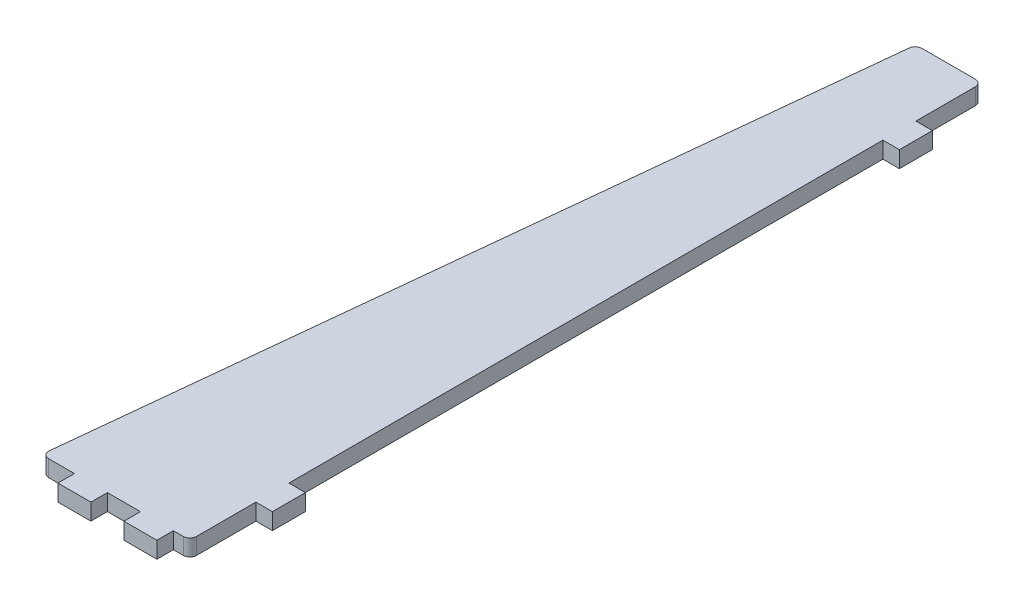
SolidWorks part; units mm, degrees
material "Beech"
ref_plane "Front Plane" through (0, 0, 0) normal (0, 0, 1) x (1, 0, 0)
ref_plane "Top Plane" through (0, 0, 0) normal (0, 1, 0) x (1, 0, 0)
ref_plane "Right Plane" through (0, 0, 0) normal (1, 0, 0) x (0, 0, -1)
sketch "Sketch1" plane through (0, 0, 0) normal (0, 1, 0) x (1, 0, 0)
  line L0 (0, 0) -> (12.7, 0)
  line L1 (12.7, 0) -> (12.7, -6.35)
  line L2 (12.7, -6.35) -> (25.4, -6.35)
  line L3 (25.4, -6.35) -> (25.4, 0)
  line L4 (25.4, 0) -> (38.1, 0)
  line L5 (38.1, 0) -> (38.1, -6.35)
  line L6 (38.1, -6.35) -> (50.8, -6.35)
  line L7 (50.8, -6.35) -> (50.8, 0)
  line L8 (50.8, 0) -> (57.15, 0)
  line L9 (57.15, 0) -> (57.15, 25.4)
  line L10 (57.15, 304.8) -> (31.75, 304.8)
  line L11 (31.75, 304.8) -> (0, 0)
  line L12 (57.15, 25.4) -> (63.5, 25.4)
  line L13 (63.5, 25.4) -> (63.5, 38.1)
  line L14 (63.5, 38.1) -> (57.15, 38.1)
  line L15 (57.15, 38.1) -> (57.15, 266.7)
  line L16 (57.15, 266.7) -> (63.5, 266.7)
  line L17 (63.5, 266.7) -> (63.5, 279.4)
  line L18 (63.5, 279.4) -> (57.15, 279.4)
  line L19 (57.15, 279.4) -> (57.15, 304.8)
  dimension "D1" = 12.7
  dimension "D2" = 6.35
  dimension "D3" = 25.4
  dimension "D4" = 25.4
  dimension "D5" = 12.7
  dimension "D6" = 304.8
  dimension "D7" = 25.4
  dimension "D8" = 25.4
  dimension "D9" = 6.35
extrude "Side Plate" add sketch "Sketch1" along normal blind 6.35
fillet "Fillet1" radius 2.54 4 edges at (57.15, 3.175, 0) (57.15, 3.175, -304.8) (31.75, 3.175, -304.8) (0, 3.175, 0)
equation "\"CageLeftBottomEdge\"=22.11mm"
equation "\"CageLeftTopEdge\"=22.11mm"
equation "\"CageRightBottomEdge\"=21.63mm"
equation "\"CageRightTopEdge\"=21.63mm"
equation "\"CageHeight\"=86.04mm"
equation "\"CageLength\"=73.76mm"
equation "\"CageTopScrewClearance\"=10mm"
equation "\"CageBottomScrewClearance\"=25mm"
equation "\"CageLeftTopDepth\"= 11.65mm"
equation "\"CageLeftBottomDepth\"=11.11mm"
equation "\"CageLeftTopHeight\"=8.56175mm"
equation "\"CageLeftBottomHeight\"=16mm"
equation "\"CageRightTopDepth\"= 11.05mm"
equation "\"CageRightBottomDepth\"=10.58mm"
equation "\"CageRightTopHeight\"=9.6mm"
equation "\"CageRightBottomHeight\"=15.49mm"
equation "\"CageLeftTopChannelDepth\"=2.41908mm"
equation "\"CageLeftBottomChannelDepth\"=2.588mm"
equation "\"CageLeftChannelHeight\"=11.7mm"
equation "\"CageRightTopChannelDepth\"=2.32mm"
equation "\"CageRightBottomChannelDepth\"=2.318mm"
equation "\"CageRightChannelHeight\"=10mm"
equation "\"CageChanRelHeight\"=23.99mm"
equation "\"CageChanRelDepth\"=5.492mm"
equation "\"CageChamberRadius\"=16.261mm"
equation "\"CageScrewDiameter\"=4.8mm"
equation "\"CageSetScrewDiameter\"=3.5mm"
equation "\"CageAxleRadius\"=6.639mm"
equation "\"CageAxleKeyHeight\"=1.619mm"
equation "\"CageAxleKeyWidth\"=2.662mm"
equation "\"CageHoseWindowWidth\"=16.29mm"
equation "\"CageHoseWindowHeight\"=26.5mm"
equation "\"CageHoseWindow-Edge\"=8.89mm"
equation "\"CageScrew-VerticalEdge\"=5.0mm"
equation "\"CageScrew-HorizontalEdge\"=7.5mm"
equation "\"CageScrew-HoseCornerScrewEdge\"=4.45mm"
equation "\"CageAxle-BottomEdge\"=56.05mm"
equation "\"CageAxle-FrontEdge\"=46.03mm"
equation "\"CageBackSetScrew-Axle\"=40mm"
equation "\"CageFrontSetScrew-Axle\"=22mm"
equation "\"CageVelocityWindow-BackEdge\"=34.8mm"
equation "\"CageVelocityWindow-BottomEdge\"=27.55mm"
equation "\"CageVelocityWindowHeight\"=22.29mm"
equation "\"CageVelocityWindowWidth\"=12.61mm"
equation "\"TriggerSlot-BottomEdge\"=6.35mm"
equation "\"TriggerSlot-FrontEdge\"=15mm"
equation "\"TriggerSlotSize\"=6.7mm"
equation "\"TriggerRackOffset\"=6mm"
equation "\"TriggerSlotSizeInt\"=.25in"
equation "\"MotorMountLegLength\"=.25in"
equation "\"GearOffset\"=.264907in"
equation "\"TriggerSlotSpacing\"=.25in"
equation "\"TriggerMiniSlotWidth\"=3.5mm"
equation "\"TriggerRackWidth\"=6.5mm"
equation "\"pandiscradius\"=14in"
equation "\"towermaterialwidth\"=.25in"
equation "\"towerslotlength\"=.5in"
equation "\"towermarkerspace\"=5in"
equation "\"towerslothorizoffset\"=1in"
equation "\"towerslothorizspacing\"=2in"
equation "\"towerslotvertoffset\"=3in"
equation "\"D1@Sketch1\"=\"towerslotlength\""
equation "\"D2@Sketch1\"=\"towermaterialwidth\""
equation "\"towerupslot\"=1in"
equation "\"D3@Sketch1\"=\"towerupslot\""
equation "\"towerslotvertspacing\"=1in"
equation "\"D4@Sketch1\"=\"towerslotvertspacing\""
equation "\"D5@Sketch1\"=\"towerslotlength\""
equation "\"towerheight\"=12in"
equation "\"D6@Sketch1\"=\"towerheight\""
equation "\"D7@Sketch1\"=\"towerslotlength\"*2"
equation "\"D8@Sketch1\"=\"towerupslot\""
equation "\"D9@Sketch1\"=\"towerslotvertoffset\"-(\"towermarkerspace\"/2)-\"towermaterialwidth\""
equation "\"D1@Side Plate\"=\"towermaterialwidth\""
equation "\"toweraxle\"=.5in"
equation "\"stepperouterrad\"=10mm"
equation "\"stepperscrewsize\"=3.45mm"
equation "\"stepperscrewc2c\"=49.5mm"
equation "\"stepperdepthoffset\"=24mm"
equation "\"stepperhorizoffset\"=22.91mm"
equation "\"shaftslotOD\"=18.8mm"
equation "\"shaftslotID\"=13.28mm"
equation "\"shaftkeywidth\"=2.67mm"
equation "\"shaftkeydepth\"=1.8mm"
equation "\"shaftcollartotaldepth\"=12.5mm"
equation "\"shaftsquaredepth\"=6mm"
equation "\"shaftsetscrewsize\"=3.5mm"
equation "\"shaftkeytightdepth\"=1.85mm"
equation "\"shaftslottightID\"=12.78mm"
equation "\"shaftsetscrewoffset\"=9mm"
equation "\"cagecollartotaldepth\"=10mm"
equation "\"cagecollartotalwidth\"=35mm"
equation "\"cagecollarbasedepth\"=4mm"
equation "\"gearhubintdiam\"=30mm"
equation "\"gearhubintwid\"=15mm"
equation "\"towerspeedwidth\"=2in"
equation "\"towerspeedheight\"=8in"
equation "\"towerspeedgap\"=2in"
equation "\"stepperaxleflat\"=.037in"
equation "\"stepperaxlerad\"=0.11811024in"
equation "\"ajaxaxlesize\"=3.87mm"
equation "\"ajaxinnercut\"=2.3mm"
equation "\"ajaxwidth\"=6.1mm"
equation "\"ajaxdiametral\"=25.8854"
equation "\"ajaxcutoutdepth\"=2.3mm"
equation "\"ajax4020gap\"=29.5mm"
equation "\"ajax4010gap\"=24.5mm"
equation "\"ajax20hubbuffer\"=6.1mm"
equation "\"ajax20hubholeoffset\"=.19685in"
equation "\"ajax20hubholesize\"=.059055in"
equation "\"ajax20cutoutint\"=13.4mm"
equation "\"ajax40hubholesize\"=7.21mm"
equation "\"ajax40hubholeoffset\"=10mm"
equation "\"ajax40hubbuffer\"=8.9mm"
equation "\"ajax40cutoutint\"=32.6mm"
equation "\"bearingpandiscrad\"=6.8in"
equation "\"bearingpandiscang\"=48.75deg"
equation "\"bearingclearholedist\"=4.7345in"
equation "\"bearingclearholesize\"=.5in"
equation "\"bearingclearholeang\"=22.5deg"
equation "\"bearingmountholedist\"=4.25in"
equation "\"bearingwirehole\"=1.5in"
equation "\"no6diam\"=.146in"
equation "\"shortconangle\"=20deg"
equation "\"shortconlen\"=.875in"
equation "\"longconlen\"=1.25in"
equation "\"longconangle\"=15deg"
